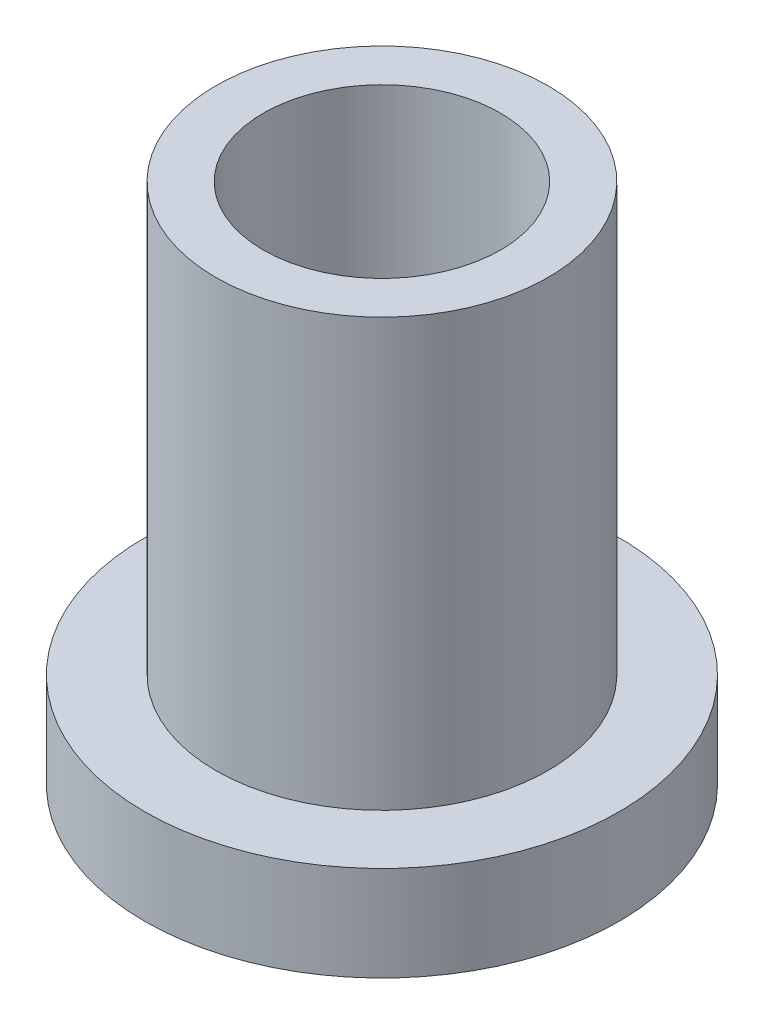
SolidWorks part; units mm, degrees
ref_plane "Front Plane" through (0, 0, 0) normal (0, 0, 1) x (1, 0, 0)
ref_plane "Top Plane" through (0, 0, 0) normal (0, 1, 0) x (1, 0, 0)
ref_plane "Right Plane" through (0, 0, 0) normal (1, 0, 0) x (0, 0, -1)
sketch "Эскиз1" plane through (0, 0, 0) normal (0, 1, 0) x (1, 0, 0)
  circle A0 centre (0, 0) radius 5
  dimension "D1" = 10
extrude "Бобышка-Вытянуть1" add sketch "Эскиз1" along normal blind 2
sketch "Эскиз2" plane through (0, 2, 0) normal (0, 1, 0) x (1, 0, 0)
  circle A0 centre (0, 0) radius 3.5
  dimension "D1" = 7
extrude "Бобышка-Вытянуть2" add sketch "Эскиз2" along normal blind 9
sketch "Эскиз3" plane through (0, 11, 0) normal (0, 1, 0) x (1, 0, 0)
  circle A0 centre (0, 0) radius 2.5
extrude "Вырез-Вытянуть1" cut sketch "Эскиз3" against normal through all
